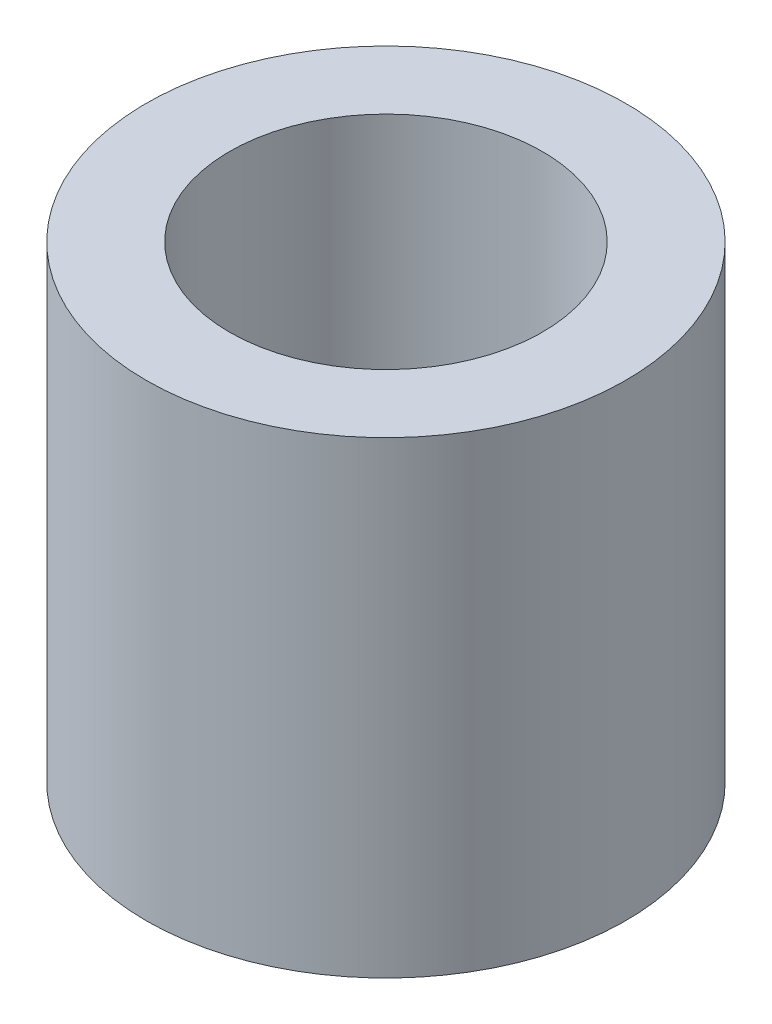
SolidWorks part; units mm, degrees
ref_plane "Front Plane" through (0, 0, 0) normal (0, 0, 1) x (1, 0, 0)
ref_plane "Top Plane" through (0, 0, 0) normal (0, 1, 0) x (1, 0, 0)
ref_plane "Right Plane" through (0, 0, 0) normal (1, 0, 0) x (0, 0, -1)
sketch "Sketch1" plane through (0, 0, 0) normal (0, 1, 0) x (1, 0, 0)
  circle A0 centre (0, 0) radius 2.675
  circle A1 centre (0, 0) radius 4.1
  dimension "D1" = 5.35
  dimension "D2" = 8.2
extrude "Boss-Extrude1" add sketch "Sketch1" along normal blind 8
